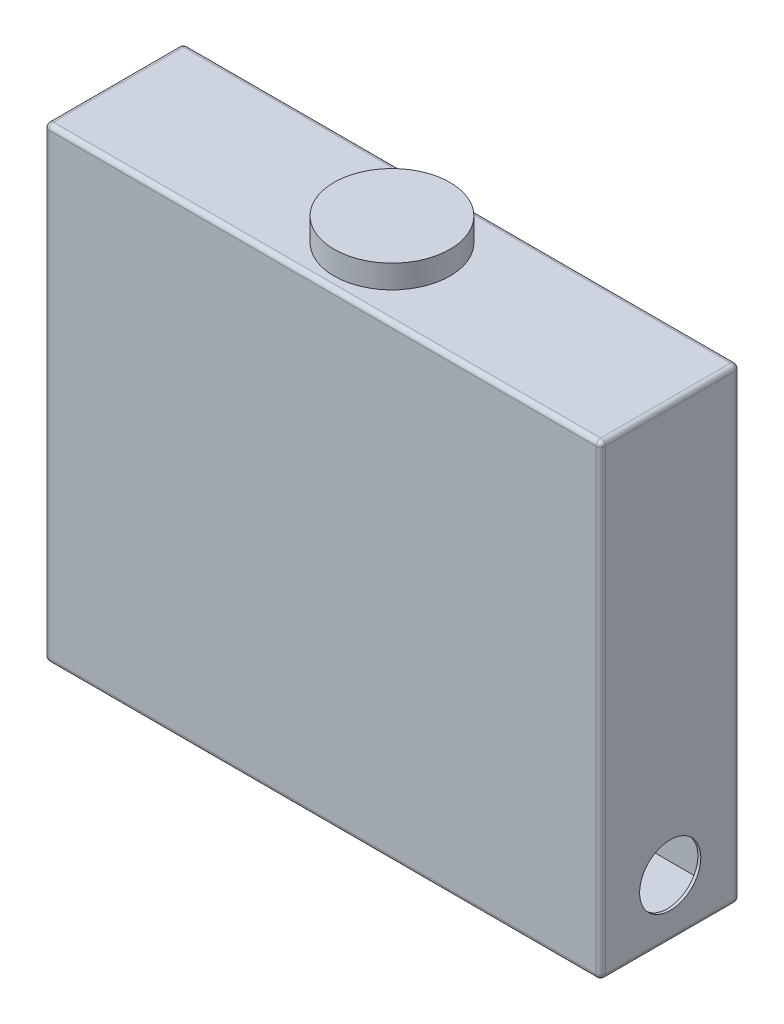
SolidWorks part; units mm, degrees
material "PE High Density Film"
ref_plane "Front Plane" through (0, 0, 0) normal (0, 0, 1) x (1, 0, 0)
ref_plane "Top Plane" through (0, 0, 0) normal (0, 1, 0) x (1, 0, 0)
ref_plane "Right Plane" through (0, 0, 0) normal (1, 0, 0) x (0, 0, -1)
sketch "Sketch1" plane through (0, 0, 0) normal (0, 1, 0) x (1, 0, 0)
  line L1 (0, 0) -> (304.8, 0)
  line L2 (0, 0) -> (0, 76.2)
  line L3 (0, 76.2) -> (304.8, 76.2)
  line L4 (304.8, 0) -> (304.8, 76.2)
  dimension "D1" = 76.2
  dimension "D2" = 304.8
extrude "Boss-Extrude1" add sketch "Sketch1" along normal blind 254
shell "Shell1" thickness 1.5875
sketch "Sketch2" plane through (0, 254, 0) normal (0, 1, 0) x (1, 0, 0)
  line L1 (0, 76.2) -> (304.8, 76.2)
  line L2 (0, 76.2) -> (0, 0)
  line L3 (0, 0) -> (304.8, 0)
  line L4 (304.8, 76.2) -> (304.8, 0)
extrude "Boss-Extrude2" add sketch "Sketch2" along normal blind 1.5875
fillet "Fillet1" radius 2.54 12 edges at (0, 0, -38.1) (0, 127.7938, -76.2) (152.4, 0, -76.2) (304.8, 127.7938, -76.2) (304.8, 0, -38.1) (152.4, 255.5875, -76.2) (304.8, 255.5875, -38.1) (0, 255.5875, -38.1) (0, 127.7938, 0) (152.4, 255.5875, 0) (304.8, 127.7938, 0) (152.4, 0, 0)
sketch "Sketch3" plane through (304.8, 0, 0) normal (1, 0, 0) x (0, 0, -1)
  line L0 (38.1, 0) -> (38.1, 255.5875) construction
  line L1 (73.66, 0) -> (2.54, 0) construction
  line L2 (2.54, 255.5875) -> (73.66, 255.5875) construction
  circle A0 centre (38.1, 31.75) radius 16.764
  point P8 (0, 0)
  dimension "D1" = 33.528
  dimension "D2" = 31.75
extrude "Cut-Extrude1" cut sketch "Sketch3" against normal up to next
sketch "Sketch4" plane through (0, 255.5875, 0) normal (0, 1, 0) x (1, 0, 0)
  line L0 (152.4, 76.2) -> (152.4, 0) construction
  line L1 (2.54, 76.2) -> (302.26, 76.2) construction
  line L2 (302.26, 0) -> (2.54, 0) construction
  circle A0 centre (152.4, 38.1) radius 28.575
  dimension "D1" = 57.15
extrude "Cut-Extrude2" cut sketch "Sketch4" against normal up to next
sketch "Sketch5" plane through (0, 255.5875, 0) normal (0, 1, 0) x (1, 0, 0)
  circle A0 centre (152.4, 38.1) radius 31.75
  dimension "D1" = 63.5
extrude "Boss-Extrude3" add sketch "Sketch5" along normal blind 12.7 separate body
